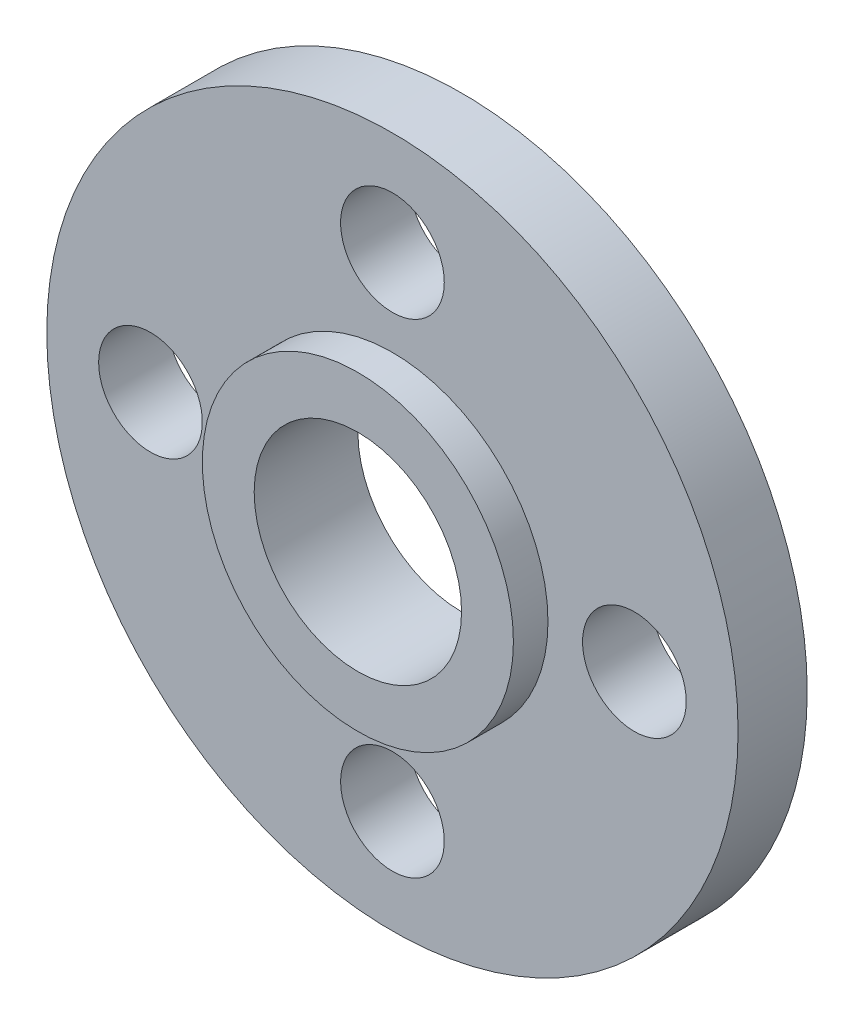
SolidWorks part; units mm, degrees
ref_plane "前视基准面" through (0, 0, 0) normal (0, 0, 1) x (1, 0, 0)
ref_plane "上视基准面" through (0, 0, 0) normal (0, 1, 0) x (1, 0, 0)
ref_plane "右视基准面" through (0, 0, 0) normal (1, 0, 0) x (0, 0, -1)
sketch "草图1" plane through (0, 0, 0) normal (0, 0, 1) x (1, 0, 0)
  circle A0 centre (0, 0) radius 10
extrude "凸台-拉伸1" add sketch "草图1" along normal blind 2
sketch "草图2" plane through (0, 0, 2) normal (0, 0, 1) x (1, 0, 0)
  circle A0 centre (0, 7) radius 1.5
  circle A1 centre (7, 0) radius 1.5
  circle A2 centre (0, -7) radius 1.5
  circle A3 centre (-7, 0) radius 1.5
extrude "切除-拉伸1" cut sketch "草图2" against normal blind 2
sketch "草图3" plane through (0, 0, 2) normal (0, 0, 1) x (1, 0, 0)
  circle A0 centre (0, 0) radius 3
extrude "切除-拉伸2" cut sketch "草图3" against normal blind 2
sketch "草图4" plane through (0, 0, 2) normal (0, 0, 1) x (1, 0, 0)
  circle A0 centre (0, 0) radius 4.5
  circle A1 centre (0, 0) radius 3
extrude "凸台-拉伸4" add sketch "草图4" along normal blind 1
